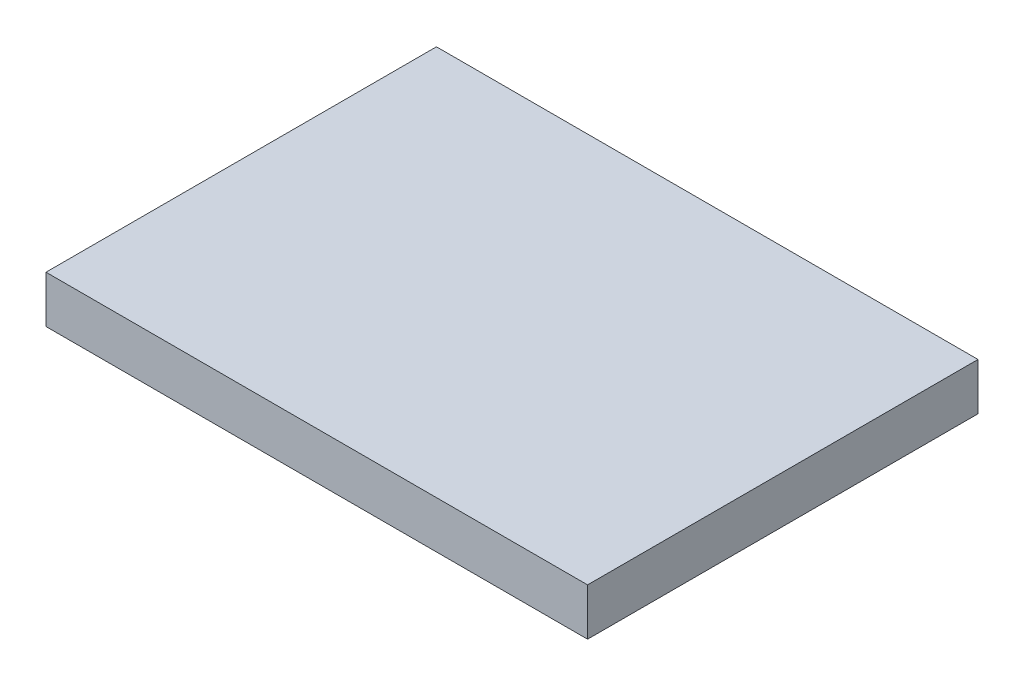
SolidWorks part; units mm, degrees
ref_plane "Front" through (0, 0, 0) normal (0, 0, 1) x (1, 0, 0)
ref_plane "Top" through (0, 0, 0) normal (0, 1, 0) x (1, 0, 0)
ref_plane "Right" through (0, 0, 0) normal (1, 0, 0) x (0, 0, -1)
sketch "Sketch1" plane through (0, 0, 0) normal (0, 1, 0) x (1, 0, 0)
  line L1 (0, 0) -> (54.8016, 0)
  line L2 (0, 0) -> (0, 39.5081)
  line L3 (0, 39.5081) -> (54.8016, 39.5081)
  line L4 (54.8016, 0) -> (54.8016, 39.5081)
extrude "Boss-Extrude1" add sketch "Sketch1" along normal blind 4.7625
